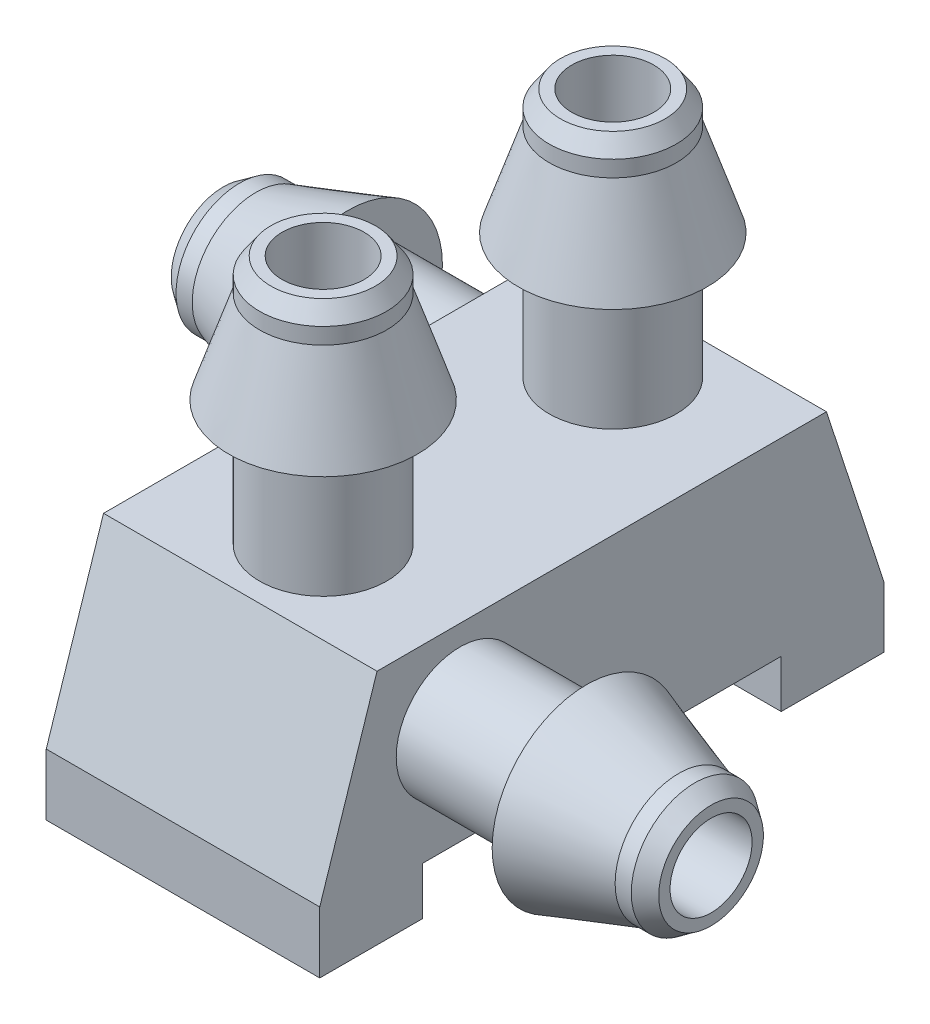
SolidWorks part; units mm, degrees
ref_plane "Front Plane" through (0, 0, 0) normal (0, 0, 1) x (1, 0, 0)
ref_plane "Top Plane" through (0, 0, 0) normal (0, 1, 0) x (1, 0, 0)
ref_plane "Right Plane" through (0, 0, 0) normal (1, 0, 0) x (0, 0, -1)
sketch "Sketch3" plane through (0, 0, 0) normal (1, 0, 0) x (0, 0, -1)
  line L0 (-19.961, -8.5376) -> (-14.7123, -8.5376)
  line L1 (-21.461, -8.3376) -> (-20.6231, -5.7709)
  line L2 (-14.7123, -8.5376) -> (-14.7123, -9.2376)
  line L3 (-14.7123, -9.2376) -> (-13.2123, -9.2376)
  line L4 (-13.2123, -9.2376) -> (-13.2123, -8.3376)
  line L5 (-13.2123, -8.3376) -> (-14.0502, -5.7709)
  line L6 (-21.461, -9.2376) -> (-21.461, -8.3376)
  line L7 (-19.961, -9.2376) -> (-21.461, -9.2376)
  line L8 (-14.0502, -5.7709) -> (-20.6231, -5.7709)
  line L9 (-17.3366, -6.3376) -> (-17.3366, -10.0275) construction
  line L10 (-19.961, -8.5376) -> (-19.961, -9.2376)
extrude "Boss-Extrude2" add sketch "Sketch3" along normal blind 4
ref_plane "Plane1" through (2, 0, 0) normal (1, 0, 0) x (0, 0, -1)
sketch "Sketch4" plane through (2, 0, 0) normal (1, 0, 0) x (0, 0, -1)
  line L0 (-20.8207, -8.0064) -> (-20.7132, -7.6942)
  line L1 (-22.6671, -7.3707) -> (-22.3611, -7.7718)
  line L2 (-21.8797, -7.6418) -> (-21.5736, -8.043)
  line L3 (-23.007, -6.9044) -> (-23.1145, -7.2166)
  line L4 (-23.007, -6.9044) -> (-20.7132, -7.6942)
  line L5 (-21.3907, -7.8102) -> (-20.8207, -8.0064)
  line L6 (-22.1767, -7.5395) -> (-21.8797, -7.6418)
  line L7 (-22.6671, -7.3707) -> (-23.1145, -7.2166)
  line L8 (-22.3611, -7.7718) -> (-22.2678, -7.804)
  line L9 (-20.5178, -7.1269) -> (-22.5583, -6.4243) construction
  line L10 (-22.2678, -7.804) -> (-22.1767, -7.5395)
  line L11 (-21.5736, -8.043) -> (-21.4817, -8.0746)
  line L12 (-21.4817, -8.0746) -> (-21.3907, -7.8102)
revolve "Revolve1" [suppressed] add sketch "Sketch4" angle 360 about L9
sketch "Sketch5" plane through (2, 0, 0) normal (1, 0, 0) x (0, 0, -1)
  line L0 (-20.3419, -5.8395) -> (-20.0116, -5.8395) construction
  line L1 (-20.3419, -3.6867) -> (-20.6216, -4.1066) construction
  line L2 (-20.3419, -4.5195) -> (-20.6216, -4.9395) construction
  line L3 (-20.0116, -3.2135) -> (-20.3419, -3.2135) construction
  line L4 (-20.0116, -3.2135) -> (-20.0116, -5.8395) construction
  line L5 (-20.3419, -5.0367) -> (-20.3419, -5.8395) construction
  line L6 (-20.3419, -4.2053) -> (-20.3419, -4.5195) construction
  line L7 (-20.3419, -3.6867) -> (-20.3419, -3.2135) construction
  line L8 (-20.6216, -4.1066) -> (-20.6216, -4.2053) construction
  line L9 (-19.4116, -5.6395) -> (-19.4116, -3.4815) construction
  line L10 (-20.6216, -4.2053) -> (-20.3419, -4.2053) construction
  line L11 (-20.6216, -4.9395) -> (-20.6216, -5.0367) construction
  line L12 (-20.6216, -5.0367) -> (-20.3419, -5.0367) construction
  line L13 (-20.3419, -5.8395) -> (-20.0116, -5.8395)
  line L14 (-20.3419, -2.3529) -> (-20.1767, -2.1163)
  line L15 (-20.3419, -2.5895) -> (-20.3419, -2.3529)
  line L16 (-20.1767, -2.1163) -> (-20.0116, -2.1163)
  line L17 (-20.0116, -2.1163) -> (-20.0116, -5.8395)
  line L18 (-20.3419, -3.9395) -> (-20.3419, -5.8395)
  line L19 (-20.3419, -3.9395) -> (-20.7902, -3.9395)
  line L20 (-20.7902, -3.9395) -> (-20.3419, -2.5895)
  line L21 (-19.4116, -4.5423) -> (-19.4116, -2.3843) construction
revolve "Revolve2" add sketch "Sketch5" angle 360 about L9
sketch "Sketch6" plane through (2, 0, 0) normal (1, 0, 0) x (0, 0, -1)
  line L0 (-16.1058, -6.0652) -> (-15.7755, -6.0652) construction
  line L1 (-16.1058, -3.9152) -> (-16.3855, -4.3351) construction
  line L2 (-16.1058, -4.748) -> (-16.3855, -5.168) construction
  line L3 (-15.7755, -3.442) -> (-16.1058, -3.442) construction
  line L4 (-15.7755, -3.442) -> (-15.7755, -6.0652) construction
  line L5 (-16.1058, -5.2652) -> (-16.1058, -6.0652) construction
  line L6 (-16.1058, -4.4338) -> (-16.1058, -4.748) construction
  line L7 (-16.1058, -3.9152) -> (-16.1058, -3.442) construction
  line L8 (-16.3855, -4.3351) -> (-16.3855, -4.4338) construction
  line L9 (-15.1755, -6.068) -> (-15.1755, -3.91) construction
  line L10 (-16.3855, -4.4338) -> (-16.1058, -4.4338) construction
  line L11 (-16.3855, -5.168) -> (-16.3855, -5.2652) construction
  line L12 (-16.3855, -5.2652) -> (-16.1058, -5.2652) construction
  line L13 (-16.1058, -5.8396) -> (-15.7755, -5.8396)
  line L14 (-16.1058, -2.353) -> (-15.9407, -2.1164)
  line L15 (-16.1058, -2.5896) -> (-16.1058, -2.353)
  line L16 (-15.9407, -2.1164) -> (-15.7755, -2.1164)
  line L17 (-15.7755, -2.1164) -> (-15.7755, -5.8396)
  line L18 (-16.1058, -3.9396) -> (-16.1058, -5.8396)
  line L19 (-16.1058, -3.9396) -> (-16.5542, -3.9396)
  line L20 (-16.5542, -3.9396) -> (-16.1058, -2.5896)
  line L21 (-15.1755, -4.5424) -> (-15.1755, -2.3844) construction
revolve "Revolve3" add sketch "Sketch6" angle 360 about L9
sketch "Sketch7" plane through (2, 0, 0) normal (1, 0, 0) x (0, 0, -1)
  line L0 (-14.4218, -6.2515) -> (-14.3197, -6.5656)
  line L1 (-12.5645, -5.6481) -> (-13.0504, -5.5119)
  line L2 (-13.3566, -5.9054) -> (-13.8424, -5.7692)
  line L3 (-12.0125, -5.816) -> (-12.1145, -5.5019)
  line L4 (-12.0125, -5.816) -> (-14.3197, -6.5656)
  line L5 (-13.8485, -6.0653) -> (-14.4218, -6.2515)
  line L6 (-13.0578, -5.8084) -> (-13.3566, -5.9054)
  line L7 (-12.5645, -5.6481) -> (-12.1145, -5.5019)
  line L8 (-13.0504, -5.5119) -> (-13.1442, -5.5424)
  line L9 (-14.1343, -7.1363) -> (-12.0819, -6.4694) construction
  line L10 (-13.1442, -5.5424) -> (-13.0578, -5.8084)
  line L11 (-13.8424, -5.7692) -> (-13.9349, -5.7993)
  line L12 (-13.9349, -5.7993) -> (-13.8485, -6.0653)
revolve "Revolve4" [suppressed] add sketch "Sketch7" angle 360 about L9
sketch "Sketch8" [suppressed] plane through (0, 5.3808, 16.4826) normal (0, 0.3103, 0.9506) x (1, 0, 0)
  ellipse E0 centre (1.5, -13.1416) end of major axis (1.5, -13.7417) minor radius 0.6 construction
  ellipse E1 centre (1.5, -13.1416) end of major axis (1.5, -13.7417) minor radius 0.6
extrude "Cut-Extrude2" [suppressed] cut sketch "Sketch8" against normal blind 1.4
sketch "Sketch10" plane through (0, -5.7709, 0) normal (0, 1, 0) x (1, 0, 0)
  circle A4 centre (2, -19.4116) radius 0.6
  circle A5 centre (2, -15.1755) radius 0.6
fillet "Fillet1" [suppressed] radius 0.5
sketch "Sketch11" [suppressed] plane through (0, -4.8483, 14.8514) normal (0, 0.3103, -0.9506) x (-1, 0, 0)
  circle A0 centre (-1.5, -2.3976) radius 0.6 construction
  circle A1 centre (-1.5, -2.3976) radius 0.6
extrude "Cut-Extrude4" [suppressed] cut sketch "Sketch11" against normal blind 1.4
fillet "Fillet2" [suppressed] radius 0.5
chamfer "Chamfer1" [suppressed] distance 0.09 angle 79
ref_plane "Plane2" through (0, -7, 0) normal (0, 1, 0) x (1, 0, 0)
sketch "Sketch12" plane through (0, -7, 0) normal (0, 1, 0) x (1, 0, 0)
  line L0 (0, -16.0758) -> (0, -15.7455)
  line L1 (-3.4866, -16.0758) -> (-3.7232, -15.9107)
  line L2 (-3.25, -16.0758) -> (-3.4866, -16.0758)
  line L3 (-3.7232, -15.9107) -> (-3.7232, -15.7455)
  line L4 (-3.7232, -15.7455) -> (0, -15.7455)
  line L5 (-1.9, -16.0758) -> (0, -16.0758)
  line L6 (-1.9, -16.0758) -> (-1.9, -16.5242)
  line L7 (-1.9, -16.5242) -> (-3.25, -16.0758)
  line L8 (-1.2972, -15.1455) -> (-3.4552, -15.1455) construction
  line L13 (0, -16.0758) -> (0, -15.7455) construction
  line L14 (-1.9528, -16.0758) -> (-1.5328, -16.3555) construction
  line L15 (-1.12, -16.0758) -> (-0.7, -16.3555) construction
  line L16 (-2.426, -15.7455) -> (-2.426, -16.0758) construction
  line L17 (-2.426, -15.7455) -> (0, -15.7455) construction
  line L18 (-0.6028, -16.0758) -> (0, -16.0758) construction
  line L19 (-1.4342, -16.0758) -> (-1.12, -16.0758) construction
  line L20 (-1.9528, -16.0758) -> (-2.426, -16.0758) construction
  line L21 (-1.5328, -16.3555) -> (-1.4342, -16.3555) construction
  line L22 (0, -15.1455) -> (-2.158, -15.1455) construction
  line L23 (-1.4342, -16.3555) -> (-1.4342, -16.0758) construction
  line L24 (-0.7, -16.3555) -> (-0.6028, -16.3555) construction
  line L25 (-0.6028, -16.3555) -> (-0.6028, -16.0758) construction
revolve "Revolve5" add sketch "Sketch12" angle 360 about L22
sketch "Sketch13" plane through (0, -7, 0) normal (0, 1, 0) x (1, 0, 0)
  line L8 (5.2483, -19.4121) -> (7.4063, -19.4121) construction
  line L9 (3.9511, -19.4121) -> (6.1091, -19.4121) construction
  line L10 (5.8511, -20.7908) -> (7.2011, -20.3424)
  line L11 (5.8511, -20.3424) -> (5.8511, -20.7908)
  line L12 (5.8511, -20.3424) -> (3.9511, -20.3424)
  line L13 (7.6743, -20.0121) -> (3.9511, -20.0121)
  line L14 (4.5539, -20.6221) -> (4.5539, -20.3424) construction
  line L15 (4.6511, -20.6221) -> (4.5539, -20.6221) construction
  line L16 (5.3853, -20.6221) -> (5.3853, -20.3424) construction
  line L17 (5.484, -20.6221) -> (5.3853, -20.6221) construction
  line L18 (5.9039, -20.3424) -> (6.3771, -20.3424) construction
  line L19 (5.3853, -20.3424) -> (5.0711, -20.3424) construction
  line L20 (4.5539, -20.3424) -> (3.9511, -20.3424) construction
  line L21 (6.3771, -20.0121) -> (3.9511, -20.0121) construction
  line L22 (6.3771, -20.0121) -> (6.3771, -20.3424) construction
  line L23 (5.0711, -20.3424) -> (4.6511, -20.6221) construction
  line L24 (5.9039, -20.3424) -> (5.484, -20.6221) construction
  line L25 (3.9511, -20.3424) -> (3.9511, -20.0121) construction
  line L26 (7.6743, -20.1773) -> (7.6743, -20.0121)
  line L27 (7.2011, -20.3424) -> (7.4377, -20.3424)
  line L28 (7.4377, -20.3424) -> (7.6743, -20.1773)
  line L29 (3.9511, -20.3424) -> (3.9511, -20.0121)
revolve "Revolve6" add sketch "Sketch13" angle 360 about L9
sketch "Sketch14" plane through (0, 0, 0) normal (-1, 0, 0) x (0, 0, 1)
  circle A1 centre (15.1455, -7) radius 0.6 construction
  circle A2 centre (15.1455, -7) radius 0.6
extrude "Cut-Extrude5" cut sketch "Sketch14" against normal blind 2.6
sketch "Sketch15" plane through (4, 0, 0) normal (1, 0, 0) x (0, 0, -1)
  circle A1 centre (-19.4121, -7) radius 0.6 construction
  circle A2 centre (-19.4121, -7) radius 0.6
extrude "Cut-Extrude6" cut sketch "Sketch15" against normal blind 3
sketch "Sketch16" plane through (0, -5.7709, 0) normal (0, 1, 0) x (1, 0, 0)
  circle A0 centre (2, -15.1755) radius 0.6 construction
  circle A1 centre (2, -19.4116) radius 0.6 construction
  circle A2 centre (2, -15.1755) radius 0.6
  circle A3 centre (2, -19.4116) radius 0.6
extrude "Cut-Extrude7" cut sketch "Sketch16" against normal blind 2
